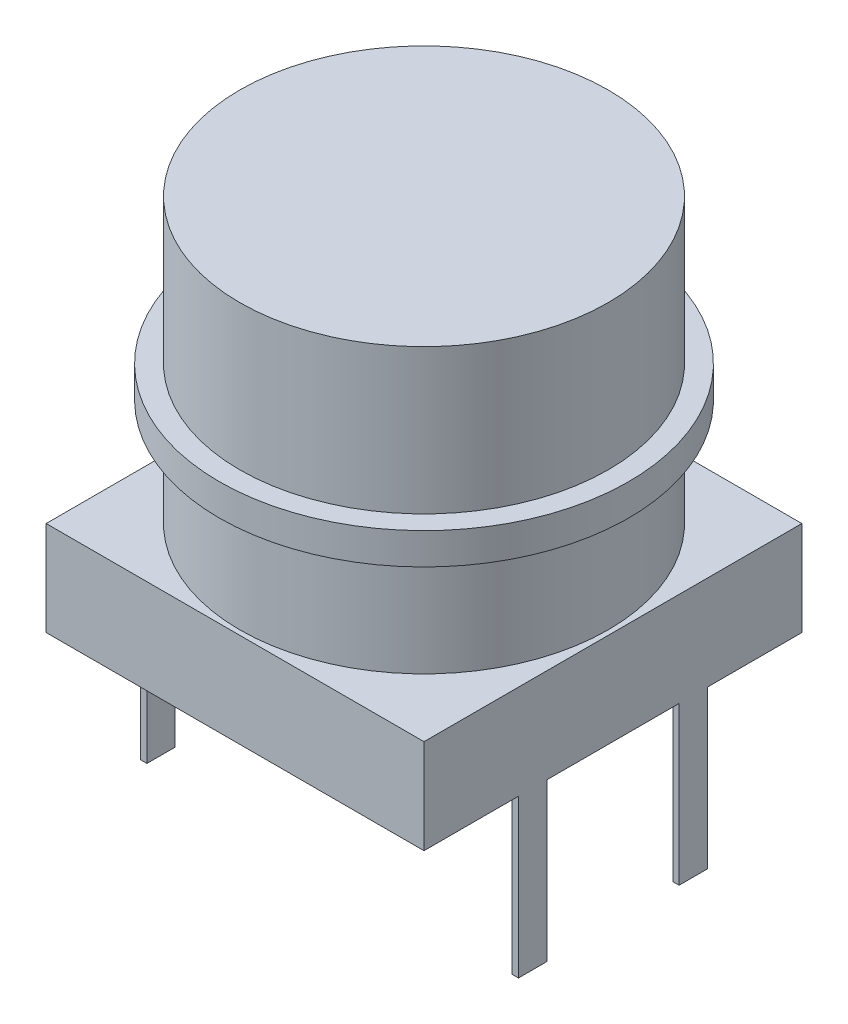
SolidWorks part; units mm, degrees
ref_plane "前视基准面" through (0, 0, 0) normal (0, 0, 1) x (1, 0, 0)
ref_plane "上视基准面" through (0, 0, 0) normal (0, 1, 0) x (1, 0, 0)
ref_plane "右视基准面" through (0, 0, 0) normal (1, 0, 0) x (0, 0, -1)
sketch "草图1" plane through (0, 0, 0) normal (0, 1, 0) x (1, 0, 0)
  line L1 (-6, 6) -> (6, 6)
  line L2 (-6, 6) -> (-6, -6)
  line L3 (-6, -6) -> (6, -6)
  line L4 (6, 6) -> (6, -6)
  line L5 (-6, 6) -> (6, -6) construction
  line L6 (-6, -6) -> (6, 6) construction
  point P0 (0, 0)
  dimension "D1" = 12
  dimension "D2" = 12
extrude "凸台-拉伸1" add sketch "草图1" along normal blind 3
sketch "草图2" plane through (0, 3, 0) normal (0, 1, 0) x (1, 0, 0)
  line L1 (-2.5, 2.5) -> (2.5, 2.5)
  line L2 (-2.5, 2.5) -> (-2.5, -2.5)
  line L3 (-2.5, -2.5) -> (2.5, -2.5)
  line L4 (2.5, 2.5) -> (2.5, -2.5)
  line L5 (-2.5, 2.5) -> (2.5, -2.5) construction
  line L6 (-2.5, -2.5) -> (2.5, 2.5) construction
  point P0 (0, 0)
  dimension "D1" = 5
  dimension "D2" = 5
extrude "凸台-拉伸2" add sketch "草图2" along normal blind 3.4
sketch "草图3" plane through (0, 6.4, 0) normal (0, 1, 0) x (1, 0, 0)
  circle A0 centre (0, 0) radius 6.5
  dimension "D1" = 13
extrude "凸台-拉伸3" add sketch "草图3" along normal blind 1
sketch "草图4" plane through (0, 7.4, 0) normal (0, 1, 0) x (1, 0, 0)
  circle A0 centre (0, 0) radius 5.85
  dimension "D1" = 11.7
extrude "凸台-拉伸4" add sketch "草图4" along normal blind 12 from surface at -7.4 starting at face at (0, 0, 0)
sketch "草图5" plane through (0, 0, 0) normal (0, -1, 0) x (1, 0, 0)
  line L0 (6, 6) -> (6, -6) construction
  line L1 (5.8, 3) -> (6, 3)
  line L2 (5.8, 3) -> (5.8, 2.1)
  line L3 (5.8, 2.1) -> (6, 2.1)
  line L4 (6, 3) -> (6, 2.1)
  line L5 (0, 0) -> (6, 0) construction
  line L6 (6, -3) -> (6, -2.1)
  line L7 (5.8, -2.1) -> (6, -2.1)
  line L8 (5.8, -3) -> (5.8, -2.1)
  line L9 (5.8, -3) -> (6, -3)
  line L10 (0, 0) -> (0, 6) construction
  line L11 (-6, 6) -> (6, 6) construction
  line L12 (-5.8, -3) -> (-6, -3)
  line L13 (-5.8, -3) -> (-5.8, -2.1)
  line L14 (-5.8, -2.1) -> (-6, -2.1)
  line L15 (-6, -3) -> (-6, -2.1)
  line L16 (-6, 3) -> (-6, 2.1)
  line L17 (-5.8, 2.1) -> (-6, 2.1)
  line L18 (-5.8, 3) -> (-5.8, 2.1)
  line L19 (-5.8, 3) -> (-6, 3)
  dimension "D1" = 0.9
  dimension "D2" = 0.2
  dimension "D3" = 6
extrude "凸台-拉伸5" add sketch "草图5" along normal blind 5
